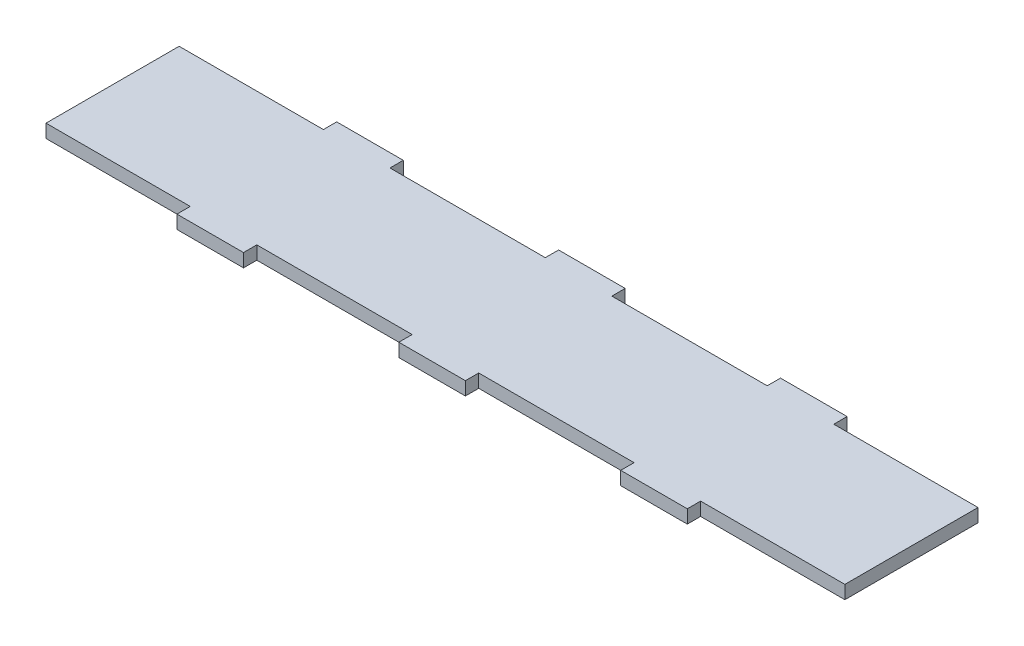
SolidWorks part; units mm, degrees
material "Acrílico (médio-alto impacto)"
ref_plane "Plano frontal" through (0, 0, 0) normal (0, 0, 1) x (1, 0, 0)
ref_plane "Plano superior" through (0, 0, 0) normal (0, 1, 0) x (1, 0, 0)
ref_plane "Plano direito" through (0, 0, 0) normal (1, 0, 0) x (0, 0, -1)
sketch "Esboço1" plane through (0, 0, 0) normal (0, 1, 0) x (1, 0, 0)
  line L0 (15, 0) -> (-15, 0)
  line L1 (-15, 0) -> (-15, 6)
  line L2 (-15, 6) -> (-85, 6)
  line L3 (-85, 6) -> (-85, 0)
  line L4 (-85, 0) -> (-115, 0)
  line L5 (-115, 0) -> (-115, 6)
  line L6 (-115, 6) -> (-180, 6)
  line L27 (-180, 66) -> (-180, 6)
  line L28 (-195.8537, 36) -> (164.1463, 36) construction
  line L29 (0, 0) -> (0, 115.2392) construction
  line L30 (180, 66) -> (180, 6)
  line L31 (115, 6) -> (180, 6)
  line L32 (115, 0) -> (115, 6)
  line L33 (85, 0) -> (115, 0)
  line L34 (85, 6) -> (85, 0)
  line L35 (15, 6) -> (85, 6)
  line L36 (15, 0) -> (15, 6)
  line L37 (15, 72) -> (15, 66)
  line L38 (15, 66) -> (85, 66)
  line L39 (85, 66) -> (85, 72)
  line L40 (85, 72) -> (115, 72)
  line L41 (115, 72) -> (115, 66)
  line L42 (115, 66) -> (180, 66)
  line L43 (-115, 66) -> (-180, 66)
  line L44 (-115, 72) -> (-115, 66)
  line L45 (-85, 72) -> (-115, 72)
  line L46 (-85, 66) -> (-85, 72)
  line L47 (-15, 66) -> (-85, 66)
  line L48 (-15, 72) -> (-15, 66)
  line L49 (15, 72) -> (-15, 72)
  point P10 (0, 0)
  point P11 (-15, 0)
  point P12 (0, 0)
  point P13 (0, 0)
  point P14 (0, 0)
  point P17 (0, 0)
  point P24 (0, 0)
  point P36 (180, 36)
  point P37 (-180, 36)
  point P43 (0, 72)
  dimension "D1" = 6
  dimension "D2" = 30
  dimension "D3" = 15
  dimension "D4" = 6
  dimension "D5" = 6
  dimension "D6" = 30
  dimension "D8" = 65
  dimension "D9" = 70
extrude "Ressalto-extrusão1" add sketch "Esboço1" along normal blind 6
